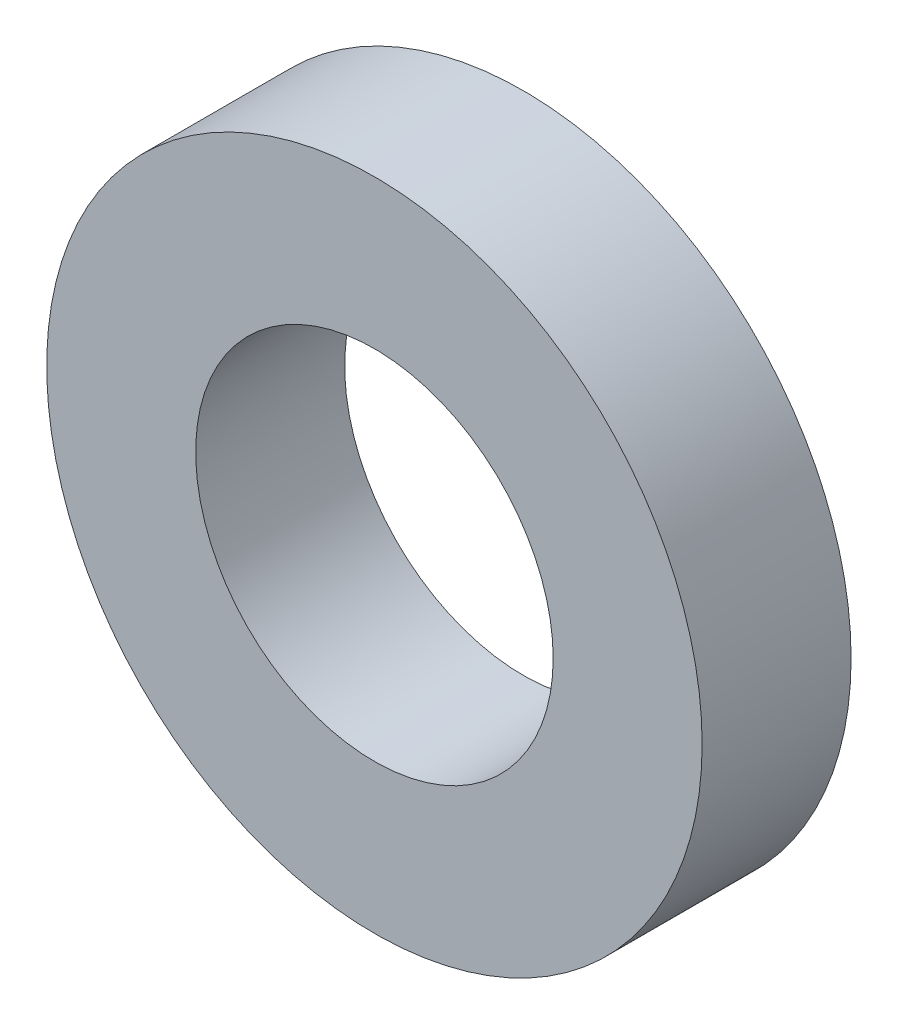
SolidWorks part; units mm, degrees
ref_plane "Front Plane" through (0, 0, 0) normal (0, 0, 1) x (1, 0, 0)
ref_plane "Top Plane" through (0, 0, 0) normal (0, 1, 0) x (1, 0, 0)
ref_plane "Right Plane" through (0, 0, 0) normal (1, 0, 0) x (0, 0, -1)
sketch "Sketch1" plane through (0, 0, 0) normal (0, 0, 1) x (1, 0, 0)
  circle A0 centre (0, 0) radius 22
  dimension "D1" = 44
extrude "Boss-Extrude1" add sketch "Sketch1" along normal blind 10
sketch "Sketch2" plane through (0, 0, 10) normal (0, 0, 1) x (1, 0, 0)
  circle A0 centre (0, 0) radius 12
  dimension "D1" = 24
extrude "Cut-Extrude1" cut sketch "Sketch2" against normal blind 25
